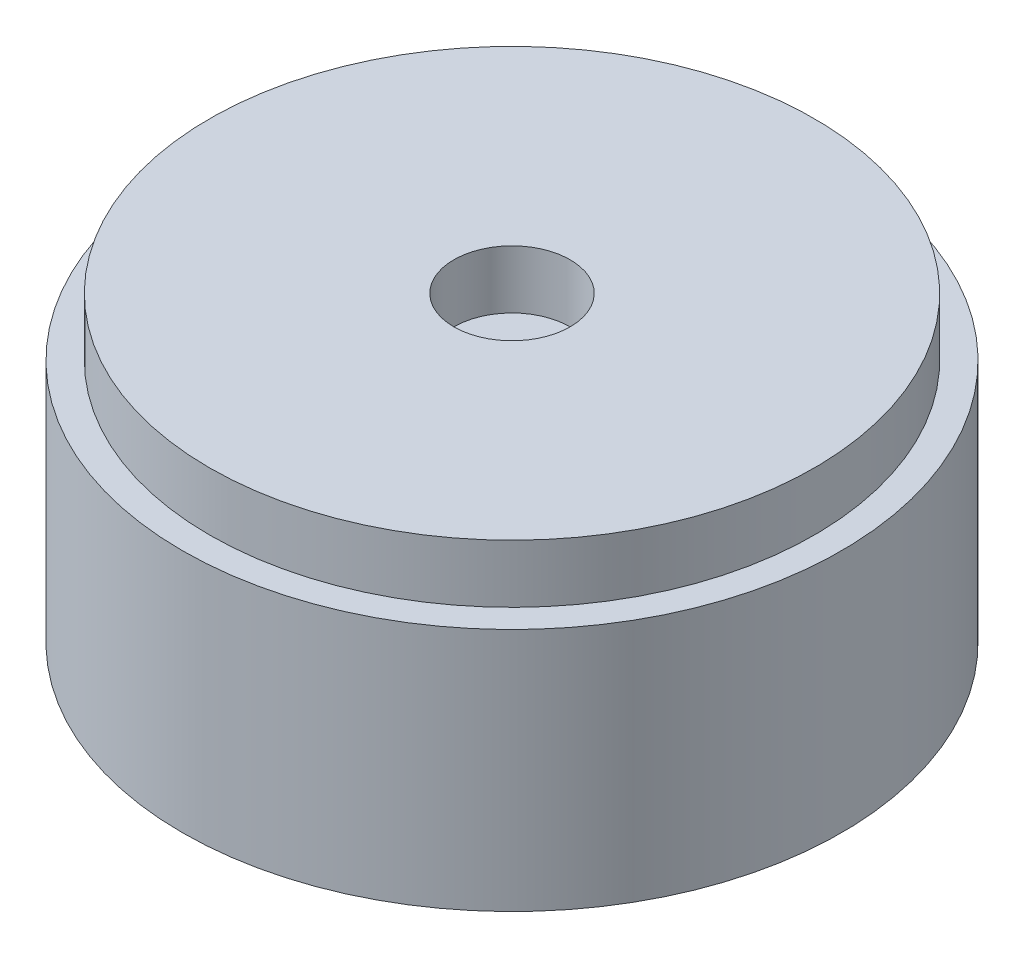
SolidWorks part; units mm, degrees
material "ABS"
ref_plane "Front Plane" through (0, 0, 0) normal (0, 0, 1) x (1, 0, 0)
ref_plane "Top Plane" through (0, 0, 0) normal (0, 1, 0) x (1, 0, 0)
ref_plane "Right Plane" through (0, 0, 0) normal (1, 0, 0) x (0, 0, -1)
sketch "Sketch1" plane through (0, 0, 0) normal (0, 1, 0) x (1, 0, 0)
  circle A0 centre (0, 0) radius 8.5
  dimension "D1" = 17
extrude "Boss-Extrude1" add sketch "Sketch1" along normal blind 7.8
sketch "Sketch2" plane through (0, 7.8, 0) normal (0, 1, 0) x (1, 0, 0)
  circle A1 centre (0, 0) radius 8.5
  circle A2 centre (0, 0) radius 8.5
  circle A3 centre (0, 0) radius 1.5
  circle A4 centre (0, 0) radius 7.8
  circle A5 centre (0, 0) radius 7.8
  circle M3 centre (0, 0) radius 8.5
  dimension "D3" = 3
  dimension "D1" = 0
  dimension "D2" = 0.7
extrude "Cut-Extrude1" cut sketch "Sketch2" against normal blind 1.5 contours A3 | A5 M3
sketch "Sketch3" plane through (0, 0, 0) normal (0, -1, 0) x (1, 0, 0)
  line L0 (-5, 5) -> (5, -5) construction
  circle A0 centre (-5, 5) radius 0.5
  circle A1 centre (5, -5) radius 0.5
  point P4 (0, 0)
  dimension "D1" = 1
  dimension "D2" = 10
  dimension "D3" = 10
extrude "Boss-Extrude2" add sketch "Sketch3" along normal blind 2
chamfer "Chamfer1" distance 0.5 distance2 0.1 2 edges at (-5, -2, 4.5) (5, -2, -5.5)
fillet "Fillet1" radius 1 2 edges at (-5, -1.5, 4.5) (5, -1.5, -5.5)
